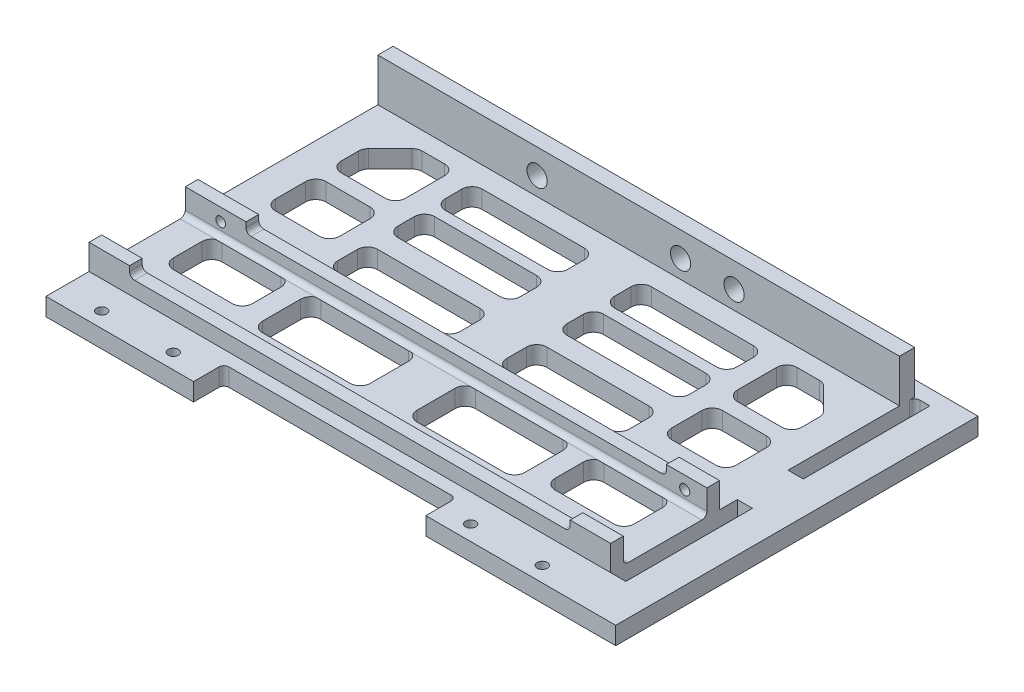
SolidWorks part; units mm, degrees
ref_plane "Front Plane" through (0, 0, 0) normal (0, 0, 1) x (1, 0, 0)
ref_plane "Top Plane" through (0, 0, 0) normal (0, 1, 0) x (1, 0, 0)
ref_plane "Right Plane" through (0, 0, 0) normal (1, 0, 0) x (0, 0, -1)
sketch "Sketch1" plane through (0, 0, 0) normal (0, 1, 0) x (1, 0, 0)
  line L1 (-51.5, -31.27) -> (51.5, -31.27)
  line L2 (-51.5, -31.27) -> (-51.5, 31.27)
  line L3 (-51.5, 31.27) -> (51.5, 31.27)
  line L4 (51.5, -31.27) -> (51.5, 31.27)
  line L5 (-51.5, -31.27) -> (51.5, 31.27) construction
  line L6 (-51.5, 31.27) -> (51.5, -31.27) construction
  point P0 (0, 0)
  dimension "D1" = 62.54
  dimension "D2" = 103
extrude "Boss-Extrude1" add sketch "Sketch1" along normal blind 3.5
sketch "Sketch2" plane through (0, 0, -31.27) normal (0, 0, -1) x (-1, 0, 0)
  line L4 (-51.5, 0) -> (51.5, 0)
  line L5 (51.5, 0) -> (51.5, 3.5)
  line L6 (51.5, 3.5) -> (-51.5, 3.5)
  line L7 (-51.5, 3.5) -> (-51.5, 0)
  line L8 (-51.5, 0) -> (51.5, 0)
  line L9 (51.5, 0) -> (51.5, 3.5)
  line L10 (51.5, 3.5) -> (-51.5, 3.5)
  line L11 (-51.5, 3.5) -> (-51.5, 0)
  dimension "D1" = 0
extrude "Boss-Extrude2" add sketch "Sketch2" along normal blind 3
sketch "Sketch5" plane through (0, 3.5, 0) normal (0, 1, 0) x (1, 0, 0)
  line L0 (51.5, 31.27) -> (43.5, 31.27)
  line L1 (51.5, -31.27) -> (51.5, 34.27) construction
  line L2 (43.5, 31.27) -> (43.5, 28.77)
  line L3 (43.5, 28.77) -> (51.5, 28.77)
  line L4 (51.5, 28.77) -> (51.5, 31.27)
  line L5 (0, -38.0579) -> (0, 51.3631) construction
  line L6 (-51.5, 34.27) -> (51.5, 34.27) construction
  dimension "D1" = 3
  dimension "D2" = 2.5
  dimension "D3" = 8
ref_plane "Plane1" through (0, 0, 0) normal (1, 0, 0) x (0, 0, -1)
sketch "Sketch8" plane through (0, 3.5, 0) normal (0, 1, 0) x (1, 0, 0)
  line L0 (51.5, -9.77) -> (-51.5, -9.77)
  line L3 (-51.5, -9.77) -> (-51.5, -7.27)
  line L4 (-51.5, -7.27) -> (51.5, -7.27)
  line L5 (51.5, -7.27) -> (51.5, -9.77)
  line L10 (-51.5, -31.27) -> (51.5, -31.27) construction
  dimension "D1" = 2.5
  dimension "D2" = 2.5
  dimension "D3" = 21.5
extrude "Boss-Extrude6" add sketch "Sketch8" along normal blind 3
sketch "Sketch9" plane through (0, 6.5, 0) normal (0, 1, 0) x (1, 0, 0)
  line L0 (51.5, -9.77) -> (43.5, -9.77)
  line L1 (-51.5, -9.77) -> (51.5, -9.77) construction
  line L2 (43.5, -9.77) -> (43.5, -7.27)
  line L3 (51.5, -7.27) -> (-51.5, -7.27) construction
  line L4 (43.5, -7.27) -> (51.5, -7.27)
  line L5 (51.5, -7.27) -> (51.5, -9.77)
  dimension "D1" = 8
extrude "Boss-Extrude7" add sketch "Sketch9" along normal blind 2
sketch "Sketch11" plane through (0, 0, 9.77) normal (0, 0, 1) x (1, 0, 0)
  line L0 (43.5, 8.5) -> (51.5, 8.5) construction
  line L1 (51.5, 8.5) -> (51.5, 3.5) construction
  circle A0 centre (47.13, 6) radius 1
  dimension "D1" = 2
  dimension "D2" = 4.37
  dimension "D3" = 2.5
extrude "Cut-Extrude3" cut sketch "Sketch11" against normal blind 22
fillet "Fillet4" radius 1 1 edges at (0, 3.5, 9.77)
sketch "Sketch12" plane through (0, 6.5, 0) normal (0, 1, 0) x (1, 0, 0)
  line L0 (-51.5, -9.77) -> (-39.5, -9.77)
  line L1 (-51.5, -9.77) -> (43.5, -9.77) construction
  line L2 (-39.5, -9.77) -> (-39.5, -7.27)
  line L3 (43.5, -7.27) -> (-51.5, -7.27) construction
  line L4 (-39.5, -7.27) -> (-51.5, -7.27)
  line L5 (-51.5, -7.27) -> (-51.5, -9.77)
  dimension "D1" = 12
extrude "Boss-Extrude8" add sketch "Sketch12" along normal blind 2
fillet "Fillet5" radius 1 1 edges at (-39.5, 6.5, 8.52)
sketch "Sketch13" plane through (0, 0, 9.77) normal (0, 0, 1) x (1, 0, 0)
  line L0 (-51.5, 8.5) -> (-51.5, 4.5) construction
  line L1 (-51.5, 8.5) -> (-39.5, 8.5) construction
  circle A0 centre (-44.5, 6) radius 0.9513
  dimension "D1" = 7
  dimension "D2" = 2.5
extrude "Cut-Extrude4" cut sketch "Sketch13" against normal blind 12
fillet "Fillet6" radius 1 1 edges at (43.5, 6.5, 8.52)
sketch "Sketch14" plane through (0, 3.5, 0) normal (0, 1, 0) x (1, 0, 0)
  line L0 (51.5, -28.77) -> (-51.5, -28.77)
  line L1 (-51.5, -28.77) -> (-51.5, -26.27)
  line L2 (-51.5, -10.77) -> (-51.5, -31.27) construction
  line L3 (-51.5, -26.27) -> (51.5, -26.27)
  line L4 (51.5, -31.27) -> (51.5, -10.77) construction
  line L5 (51.5, -26.27) -> (51.5, -28.77)
  line L6 (-51.5, -31.27) -> (51.5, -31.27) construction
  dimension "D1" = 2.5
  dimension "D2" = 2.5
extrude "Boss-Extrude9" add sketch "Sketch14" along normal blind 3
sketch "Sketch15" plane through (0, 6.5, 0) normal (0, 1, 0) x (1, 0, 0)
  line L0 (51.5, -28.77) -> (43.5, -28.77)
  line L1 (-51.5, -28.77) -> (51.5, -28.77) construction
  line L2 (43.5, -28.77) -> (43.5, -26.27)
  line L3 (51.5, -26.27) -> (-51.5, -26.27) construction
  line L4 (43.5, -26.27) -> (51.5, -26.27)
  line L5 (51.5, -26.27) -> (51.5, -28.77)
  line L6 (-51.5, -28.77) -> (-51.5, -26.27)
  line L7 (-51.5, -26.27) -> (-43.5, -26.27)
  line L8 (-43.5, -26.27) -> (-43.5, -28.77)
  line L9 (-43.5, -28.77) -> (-51.5, -28.77)
  dimension "D1" = 8
  dimension "D2" = 8
  dimension "D3" = 2.5
extrude "Boss-Extrude10" add sketch "Sketch15" along normal up to surface (2 mm away) up to face at (47.5, 8.5, 8.52)
sketch "Sketch16" plane through (0, 0, 31.27) normal (0, 0, 1) x (1, 0, 0)
  line L0 (43.5, 8.5) -> (51.5, 8.5) construction
  line L2 (51.5, 3.5) -> (51.5, 0) construction
  line L3 (-51.5, 3.5) -> (-51.5, 0) construction
  line L4 (-51.5, 8.5) -> (-43.5, 8.5) construction
  circle A0 centre (47.5, 4.5) radius 1
  circle A1 centre (-47.5, 4.5) radius 1
  dimension "D5" = 2
  dimension "D6" = 2
  dimension "D1" = 4
  dimension "D2" = 4
  dimension "D3" = 4
  dimension "D4" = 4
fillet "Fillet7" radius 1 3 edges at (0, 3.5, 26.27) (-43.5, 6.5, 27.52) (43.5, 6.5, 27.52)
sketch "Sketch17" plane through (0, 3.5, 0) normal (0, 1, 0) x (1, 0, 0)
  line L0 (43.5, -20.1173) -> (31.8853, -20.1173)
  line L1 (29.8853, -18.1173) -> (29.8853, -12.5081)
  line L2 (31.8853, -10.5081) -> (43.5, -10.5081)
  line L3 (45.5, -12.5081) -> (45.5, -18.1173)
  line L4 (25.8853, -20.1211) -> (25.8853, -12.5858)
  line L5 (23.8853, -10.5858) -> (6.6087, -10.5858)
  line L6 (4.6087, -12.5858) -> (4.6087, -20.1211)
  line L7 (6.6087, -22.1211) -> (23.8853, -22.1211)
  line L8 (44.9142, 19.849) -> (40.6192, 24.144)
  line L9 (39.205, 24.7298) -> (34.7808, 24.7298)
  line L10 (32.7808, 22.7298) -> (32.7808, 15.003)
  line L11 (34.7808, 13.003) -> (43.5, 13.003)
  line L12 (45.5, 15.003) -> (45.5, 18.4348)
  line L13 (43.5, 10.003) -> (34.7808, 10.003)
  line L14 (32.7808, 8.003) -> (32.7808, 2)
  line L15 (34.7808, 0) -> (43.5, 0)
  line L16 (45.5, 2) -> (45.5, 8.003)
  line L17 (28.7808, -2.3836) -> (28.7808, 1.5152)
  line L18 (26.7808, 3.5152) -> (6.6087, 3.5152)
  line L19 (4.6087, 1.5152) -> (4.6087, -2.3836)
  line L20 (6.6087, -4.3836) -> (26.7808, -4.3836)
  line L21 (28.7808, 9.5152) -> (28.7808, 12.74)
  line L22 (26.7808, 14.74) -> (6.6087, 14.74)
  line L23 (4.6087, 12.74) -> (4.6087, 9.5152)
  line L24 (6.6087, 7.5152) -> (26.7808, 7.5152)
  line L25 (51.5, -25.27) -> (51.5, -10.77) construction
  line L26 (51.5, -7.27) -> (51.5, 34.27) construction
  line L28 (26.7808, 16.8713) -> (6.6087, 16.8713)
  line L29 (28.7808, 18.8713) -> (28.7808, 22.144)
  line L30 (26.7808, 24.144) -> (6.6087, 24.144)
  line L31 (4.6087, 18.8713) -> (4.6087, 22.144)
  arc A0 (4.6087, -2.3836) -> (6.6087, -4.3836) centre (6.6087, -2.3836) ccw
  arc A1 (28.7808, -2.3836) -> (26.7808, -4.3836) centre (26.7808, -2.3836) cw
  arc A2 (28.7808, 1.5152) -> (26.7808, 3.5152) centre (26.7808, 1.5152) ccw
  arc A3 (6.6087, 3.5152) -> (4.6087, 1.5152) centre (6.6087, 1.5152) ccw
  arc A4 (4.6087, 9.5152) -> (6.6087, 7.5152) centre (6.6087, 9.5152) ccw
  arc A5 (6.6087, 14.74) -> (4.6087, 12.74) centre (6.6087, 12.74) ccw
  arc A6 (28.7808, 12.74) -> (26.7808, 14.74) centre (26.7808, 12.74) ccw
  arc A7 (28.7808, 9.5152) -> (26.7808, 7.5152) centre (26.7808, 9.5152) cw
  arc A8 (32.7808, 15.003) -> (34.7808, 13.003) centre (34.7808, 15.003) ccw
  arc A9 (34.7808, 24.7298) -> (32.7808, 22.7298) centre (34.7808, 22.7298) ccw
  arc A10 (40.6192, 24.144) -> (39.205, 24.7298) centre (39.205, 22.7298) ccw
  arc A11 (44.9142, 19.849) -> (45.5, 18.4348) centre (43.5, 18.4348) cw
  arc A12 (43.5, 13.003) -> (45.5, 15.003) centre (43.5, 15.003) ccw
  arc A13 (32.7808, 2) -> (34.7808, 0) centre (34.7808, 2) ccw
  arc A14 (34.7808, 10.003) -> (32.7808, 8.003) centre (34.7808, 8.003) ccw
  arc A15 (43.5, 10.003) -> (45.5, 8.003) centre (43.5, 8.003) cw
  arc A16 (43.5, 0) -> (45.5, 2) centre (43.5, 2) ccw
  arc A17 (4.6087, -20.1211) -> (6.6087, -22.1211) centre (6.6087, -20.1211) ccw
  arc A18 (6.6087, -10.5858) -> (4.6087, -12.5858) centre (6.6087, -12.5858) ccw
  arc A19 (25.8853, -12.5858) -> (23.8853, -10.5858) centre (23.8853, -12.5858) ccw
  arc A20 (25.8853, -20.1211) -> (23.8853, -22.1211) centre (23.8853, -20.1211) cw
  arc A21 (31.8853, -20.1173) -> (29.8853, -18.1173) centre (31.8853, -18.1173) cw
  arc A22 (29.8853, -12.5081) -> (31.8853, -10.5081) centre (31.8853, -12.5081) cw
  arc A23 (43.5, -10.5081) -> (45.5, -12.5081) centre (43.5, -12.5081) cw
  arc A24 (43.5, -20.1173) -> (45.5, -18.1173) centre (43.5, -18.1173) ccw
  arc A25 (6.6087, 24.144) -> (4.6087, 22.144) centre (6.6087, 22.144) ccw
  arc A26 (6.6087, 16.8713) -> (4.6087, 18.8713) centre (6.6087, 18.8713) cw
  arc A27 (26.7808, 16.8713) -> (28.7808, 18.8713) centre (26.7808, 18.8713) ccw
  arc A28 (28.7808, 22.144) -> (26.7808, 24.144) centre (26.7808, 22.144) ccw
  point P30 (29.8853, -15.3127)
  point P37 (28.7808, 3.5152)
  point P40 (4.6087, 3.5152)
  point P71 (4.6087, -10.5858)
  dimension "D9" = 2
  dimension "D10" = 2
  dimension "D1" = 6
  dimension "D2" = 6
  dimension "D3" = 6
  dimension "D4" = 4
  dimension "D5" = 4
  dimension "D6" = 4
  dimension "D7" = 4
  dimension "D8" = 3
extrude "Cut-Extrude6" cut sketch "Sketch17" against normal blind 5
mirror "Mirror4" about plane through (0, 0, 0) normal (1, 0, 0) of "Cut-Extrude6"
sketch "Sketch18" plane through (0, 3.5, 0) normal (0, 1, 0) x (1, 0, 0)
  line L0 (51.5, -7.27) -> (51.5, 34.27) construction
  line L1 (51.5, 31.27) -> (-51.5, 31.27)
  line L2 (51.5, 31.27) -> (51.5, 28.27)
  line L3 (51.5, 28.27) -> (-51.5, 28.27)
  line L4 (-51.5, 31.27) -> (-51.5, 28.27)
  line L5 (-51.5, 34.27) -> (-51.5, -7.27) construction
  line L7 (-51.5, 34.27) -> (51.5, 34.27) construction
  dimension "D1" = 3
  dimension "D2" = 3
extrude "Boss-Extrude11" add sketch "Sketch18" along normal blind 8.5
sketch "Sketch20" plane through (0, 0, 31.27) normal (0, 0, 1) x (1, 0, 0)
  line L0 (-51.5, 3.5) -> (-51.5, 0)
  line L1 (-51.5, 0) -> (-22.36, 0)
  line L2 (-51.5, 0) -> (51.5, 0) construction
  line L3 (-22.36, 0) -> (-22.36, 3.5)
  line L4 (-51.5, 3.5) -> (51.5, 3.5) construction
  line L5 (-22.36, 3.5) -> (-51.5, 3.5)
  line L7 (51.5, 0) -> (23.5, 0)
  line L8 (51.5, 0) -> (51.5, 3.5)
  line L9 (51.5, 3.5) -> (23.5, 3.5)
  line L10 (23.5, 0) -> (23.5, 3.5)
  dimension "D1" = 29.14
  dimension "D2" = 28
extrude "Boss-Extrude12" add sketch "Sketch20" along normal blind 6
fillet "Fillet8" radius 1 2 edges at (23.5, 1.75, 31.27) (-22.36, 1.75, 31.27)
sketch "Sketch21" plane through (0, 0, 0) normal (0, -1, 0) x (1, 0, 0)
  line L0 (-51.5, 37.27) -> (-22.36, 37.27) construction
  line L1 (-51.5, -34.27) -> (-51.5, 37.27) construction
  line L2 (-22.36, 37.27) -> (-22.36, 32.27) construction
  circle A0 centre (-43.5, 34.27) radius 1
  circle A1 centre (-29.36, 34.27) radius 1
  point P10 (-22.36, 34.77)
  dimension "D1" = 2
  dimension "D2" = 2
  dimension "D3" = 3
  dimension "D4" = 3
  dimension "D5" = 8
  dimension "D6" = 7
extrude "Cut-Extrude7" cut sketch "Sketch21" against normal blind 6
mirror "Mirror5" about plane through (0, 0, 0) normal (1, 0, 0) of "Cut-Extrude7"
sketch "Sketch22" plane through (51.5, 0, 0) normal (1, 0, 0) x (0, 0, -1)
  line L1 (-37.27, 0) -> (34.27, 0)
  line L2 (-37.27, 0) -> (-37.27, 3.5)
  line L3 (-37.27, 3.5) -> (34.27, 3.5)
  line L4 (34.27, 0) -> (34.27, 3.5)
extrude "Boss-Extrude13" add sketch "Sketch22" along normal blind 6.5
sketch "Sketch23" plane through (0, 3.5, 0) normal (0, 1, 0) x (1, 0, 0)
  line L0 (-51.5, 34.27) -> (58, 34.27) construction
  line L1 (58, -37.27) -> (51.5, -37.27) construction
  line L2 (58, -37.27) -> (58, 34.27) construction
  line L3 (58, 34.27) -> (51.5, 34.27) construction
  line L4 (51.5, -37.27) -> (51.5, 34.27) construction
  line L5 (51.5, 31.27) -> (-51.5, 31.27) construction
  line L6 (54.5, 31.27) -> (51.5, 31.27)
  line L7 (54.5, 31.27) -> (54.5, -28.77)
  line L8 (54.5, -28.77) -> (51.5, -28.77)
  line L9 (51.5, 31.27) -> (51.5, -28.77)
  line L10 (54.5, 31.27) -> (51.5, -28.77) construction
  line L11 (54.5, -28.77) -> (51.5, 31.27) construction
  line L12 (-51.5, -28.77) -> (51.5, -28.77) construction
  line L13 (51.5, 31.27) -> (51.5, 28.27) construction
  point P7 (53, 1.25)
  dimension "D1" = 0
  dimension "D2" = 3
  dimension "D3" = 0
extrude "Cut-Extrude8" cut sketch "Sketch23" against normal blind 10
sketch "Sketch25" plane through (0, 0, -28.27) normal (0, 0, 1) x (1, 0, 0)
  circle A3 centre (-20.06, 7.1) radius 1 construction
  circle A4 centre (8.27, 7.1) radius 1 construction
  circle A5 centre (18.84, 7.1) radius 1 construction
  circle A6 centre (18.84, 7.1) radius 2
  circle A7 centre (8.27, 7.1) radius 2
  circle A8 centre (-20.06, 7.1) radius 2
  dimension "D1" = 4
  dimension "D2" = 4
  dimension "D3" = 4
extrude "Cut-Extrude9" cut sketch "Sketch25" against normal blind 10
sketch "Sketch26" plane through (0, 0, 0) normal (0, -1, 0) x (1, 0, 0)
  line L0 (54.5, -1.25) -> (51.5, -1.25) construction
  line L1 (54.5, -31.27) -> (54.5, 28.77) construction
  line L2 (51.5, 28.77) -> (51.5, -31.27) construction
  line L3 (54.5, 3.77) -> (51.5, 3.77)
  line L4 (54.5, 28.77) -> (51.5, 28.77) construction
  line L5 (54.5, -6.27) -> (51.5, -6.27)
  line L6 (51.5, -31.27) -> (54.5, -31.27) construction
  line L8 (51.5, 3.77) -> (51.5, -6.27)
  line L9 (54.5, -6.27) -> (54.5, 3.77)
  dimension "D1" = 25
  dimension "D2" = 25
extrude "Boss-Extrude14" add sketch "Sketch26" against normal up to surface (3.5 mm away) up to face at (29.36, 3.5, 33.27)
sketch "Sketch27" plane through (58, 0, 0) normal (1, 0, 0) x (0, 0, -1)
  line L4 (-37.27, 3.5) -> (-37.27, 0)
  line L5 (-37.27, 0) -> (34.27, 0)
  line L6 (34.27, 0) -> (34.27, 3.5)
  line L7 (34.27, 3.5) -> (-37.27, 3.5)
  line L8 (-37.27, 3.5) -> (-37.27, 0)
  line L9 (-37.27, 0) -> (34.27, 0)
  line L10 (34.27, 0) -> (34.27, 3.5)
  line L11 (34.27, 3.5) -> (-37.27, 3.5)
  dimension "D1" = 0
extrude "Boss-Extrude15" add sketch "Sketch27" along normal blind 3
fillet "Fillet9" radius 1 1 edges at (51.5, 1.75, -31.27)
